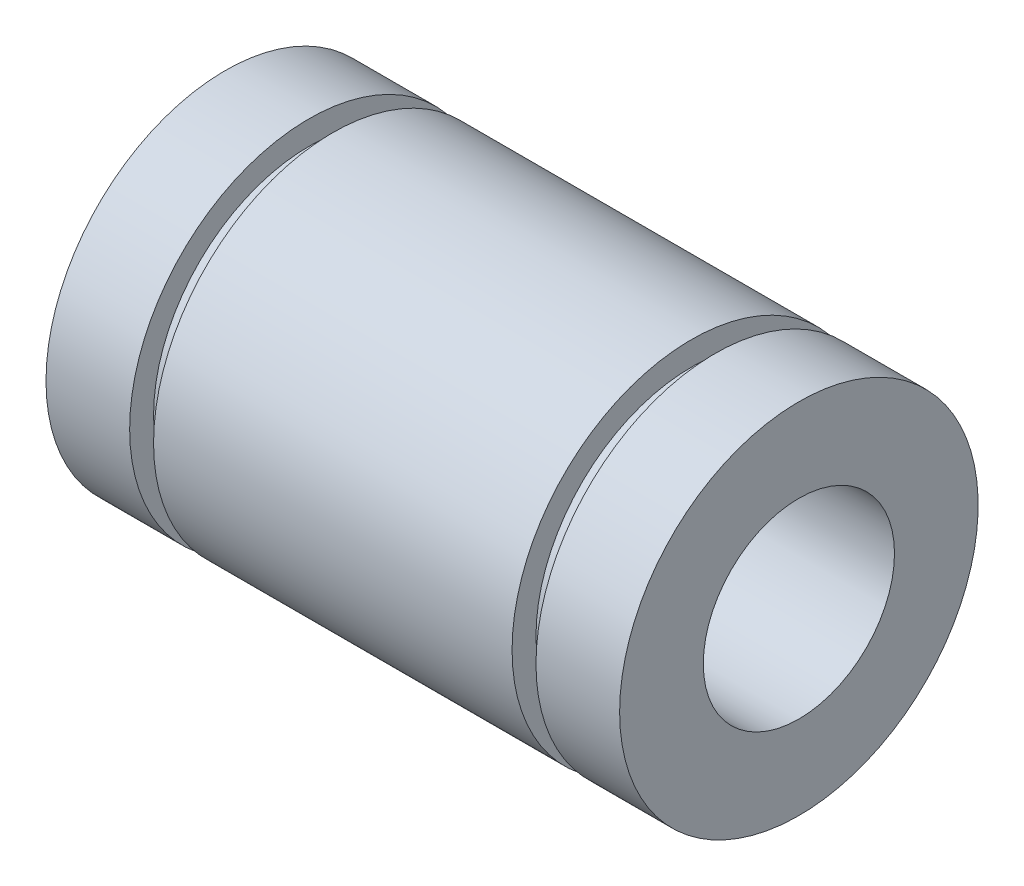
SolidWorks part; units mm, degrees
ref_plane "Alzado" through (0, 0, 0) normal (0, 0, 1) x (1, 0, 0)
ref_plane "Planta" through (0, 0, 0) normal (0, 1, 0) x (1, 0, 0)
ref_plane "Vista lateral" through (0, 0, 0) normal (1, 0, 0) x (0, 0, -1)
sketch "Croquis4" plane through (0, 0, 0) normal (0, 0, 1) x (1, 0, 0)
  line L0 (0, 0) -> (7.1387, 0) construction
  line L2 (0, 4) -> (24, 4)
  line L3 (24, 4) -> (24, 7.5)
  line L5 (24, 7.5) -> (20.5, 7.5)
  line L6 (0, 7.5) -> (0, 4)
  line L7 (3.5, 7.5) -> (3.5, 6.5)
  line L8 (20.5, 7.5) -> (20.5, 6.5)
  line L9 (4.5, 7.5) -> (4.5, 6.5)
  line L10 (19.5, 7.5) -> (19.5, 6.5)
  line L11 (4.5, 11.1852) -> (4.5, 6.5) construction
  line L12 (3.5, 11.1852) -> (3.5, 6.5) construction
  line L13 (19.5, 11.1852) -> (19.5, 6.5) construction
  line L14 (20.5, 11.1852) -> (20.5, 6.5) construction
  line L15 (19.5, 6.5) -> (20.5, 6.5)
  line L16 (4.5, 6.5) -> (3.5, 6.5)
  line L17 (3.5, 7.5) -> (0, 7.5)
  line L18 (19.5, 7.5) -> (4.5, 7.5)
  dimension "D1" = 24
  dimension "D2" = 4
  dimension "D3" = 3.5
  dimension "D4" = 3.5
  dimension "D5" = 3.5
  dimension "D8" = 1
  dimension "D9" = 1
  dimension "D6" = 1
  dimension "D7" = 1
revolve "Revolución1" add sketch "Croquis4" angle 360 about L0
